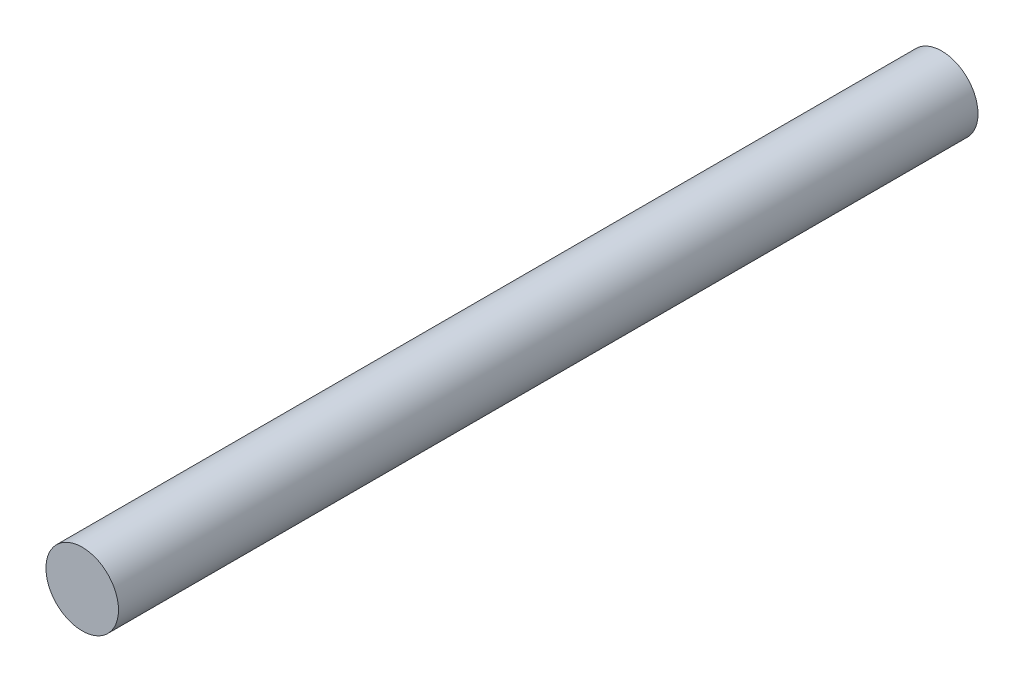
SolidWorks part; units mm, degrees
ref_plane "Front Plane" through (0, 0, 0) normal (0, 0, 1) x (1, 0, 0)
ref_plane "Top Plane" through (0, 0, 0) normal (0, 1, 0) x (1, 0, 0)
ref_plane "Right Plane" through (0, 0, 0) normal (1, 0, 0) x (0, 0, -1)
sketch "Sketch1" plane through (0, 0, 0) normal (0, 0, 1) x (1, 0, 0)
  circle A0 centre (0, 0) radius 3.8
  dimension "D1" = 7.6
extrude "Boss-Extrude1" add sketch "Sketch1" along normal blind 90
